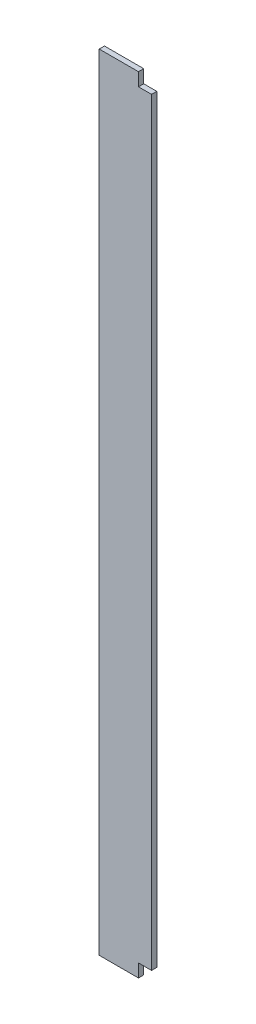
SolidWorks part; units mm, degrees
ref_plane "Plano frontal" through (0, 0, 0) normal (0, 0, 1) x (1, 0, 0)
ref_plane "Plano superior" through (0, 0, 0) normal (0, 1, 0) x (1, 0, 0)
ref_plane "Plano direito" through (0, 0, 0) normal (1, 0, 0) x (0, 0, -1)
sketch "Esboço1" plane through (0, 0, 0) normal (0, 1, 0) x (1, 0, 0)
  line L5 (-1156.4837, 804.6872) -> (-956.4837, 804.6872)
  line L6 (-1156.4837, 804.6872) -> (-1156.4837, 784.6872)
  line L7 (-1156.4837, 784.6872) -> (-956.4837, 784.6872)
  line L8 (-956.4837, 804.6872) -> (-956.4837, 784.6872)
  dimension "D1" = 200
  dimension "D2" = 20
extrude "Ressalto-extrusão1" add sketch "Esboço1" along normal blind 3000 contours L5 L8 L7 L6
sketch "Esboço2" plane through (0, 0, -784.6872) normal (0, 0, 1) x (1, 0, 0)
  line L1 (-956.4837, 0) -> (-1006.4837, 0)
  line L2 (-956.4837, 0) -> (-956.4837, 50)
  line L3 (-956.4837, 50) -> (-1006.4837, 50)
  line L4 (-1006.4837, 0) -> (-1006.4837, 50)
  dimension "D1" = 50
  dimension "D2" = 50
extrude "Corte-extrusão1" cut sketch "Esboço2" against normal through all
sketch "Esboço3" plane through (0, 0, -784.6872) normal (0, 0, 1) x (1, 0, 0)
  line L1 (-956.4837, 3000) -> (-1006.4837, 3000)
  line L2 (-956.4837, 3000) -> (-956.4837, 2950)
  line L3 (-956.4837, 2950) -> (-1006.4837, 2950)
  line L4 (-1006.4837, 3000) -> (-1006.4837, 2950)
  dimension "D1" = 50
  dimension "D2" = 50
extrude "Corte-extrusão2" cut sketch "Esboço3" against normal through all
